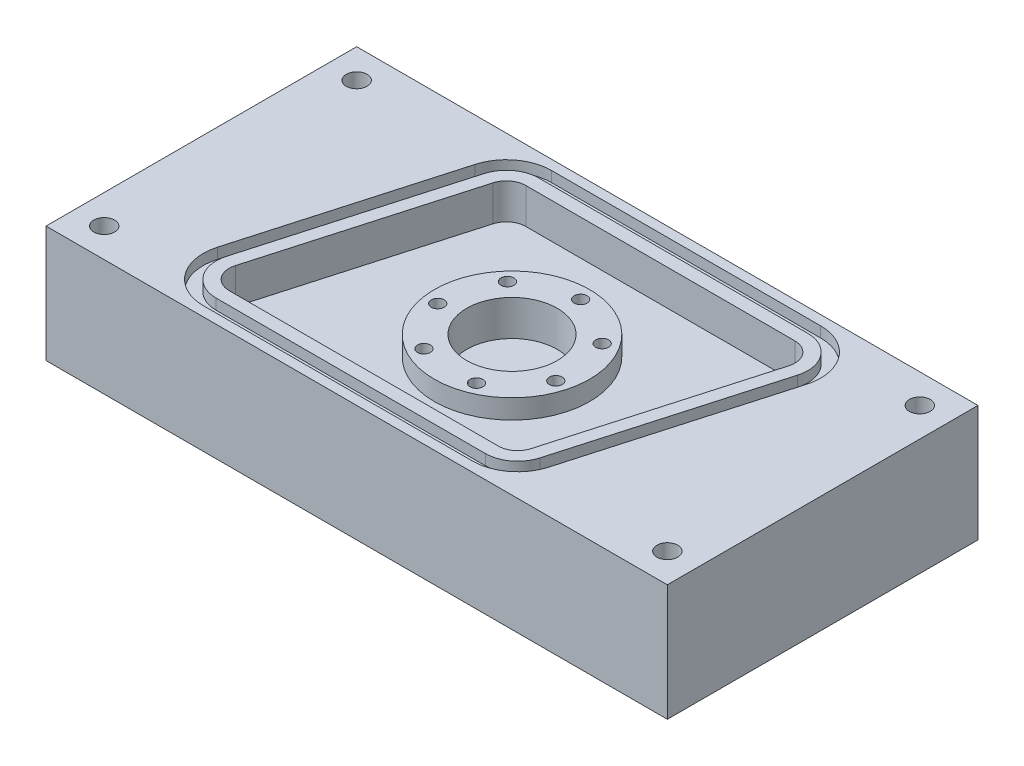
SolidWorks part; units mm, degrees
ref_plane "Front Plane" through (0, 0, 0) normal (0, 0, 1) x (1, 0, 0)
ref_plane "Top Plane" through (0, 0, 0) normal (0, 1, 0) x (1, 0, 0)
ref_plane "Right Plane" through (0, 0, 0) normal (1, 0, 0) x (0, 0, -1)
sketch "Sketch1" plane through (0, 0, 0) normal (0, 1, 0) x (1, 0, 0)
  line L1 (-76.2, 38.1) -> (76.2, 38.1)
  line L2 (-76.2, 38.1) -> (-76.2, -38.1)
  line L3 (-76.2, -38.1) -> (76.2, -38.1)
  line L4 (76.2, 38.1) -> (76.2, -38.1)
  line L5 (-76.2, 38.1) -> (76.2, -38.1) construction
  line L6 (-76.2, -38.1) -> (76.2, 38.1) construction
  point P0 (0, 0)
  dimension "D1" = 152.4
  dimension "D2" = 76.2
extrude "Boss-Extrude1" add sketch "Sketch1" along normal blind 28.575
hole_wizard "#7 (0.201) Diameter Hole1" positions "Sketch3" profile "Sketch2" hole size "#7" standard "ANSI Inch"
sketch "Sketch3" plane through (0, 28.575, 0) normal (0, 1, 0) x (-1, 0, 0)
  line L0 (76.2, -38.1) -> (76.2, 38.1) construction
  line L1 (-76.2, 38.1) -> (-76.2, -38.1) construction
  line L2 (-76.2, -38.1) -> (76.2, -38.1) construction
  line L3 (76.2, 38.1) -> (-76.2, 38.1) construction
  point P0 (69.0626, -30.9626)
  point P1 (69.0626, 30.9626)
  point P3 (-69.0626, 30.9626)
  point P5 (-69.0626, -30.9626)
  dimension "D1" = 7.1374
  dimension "D2" = 7.1374
  dimension "D3" = 7.1374
  dimension "D4" = 7.1374
  dimension "D5" = 7.1374
  dimension "D6" = 7.1374
  dimension "D7" = 7.1374
  dimension "D8" = 7.1374
sketch "Sketch2" plane through (-69.0626, 28.575, -30.9626) normal (1, 0, 0) x (0, 0, 1)
  line L0 (0, 0) -> (0, 14.2338)
  line L1 (0, 14.2338) -> (2.5527, 12.7)
  line L2 (2.5527, 12.7) -> (2.5527, 0)
  line L5 (2.5527, 0) -> (0, 0)
  line L10 (0, 14.2338) -> (-2.5527, 12.7) construction
  line L11 (0, -6.35) -> (0, 107.95) construction
  dimension "Hole Dia." = 5.1054
  dimension "Hole Depth" = 12.7
  dimension "Drill Angle" = 118
sketch "Sketch4" plane through (0, 28.575, 0) normal (0, 1, 0) x (1, 0, 0)
  line L0 (-76.2, 38.1) -> (-76.2, -38.1) construction
  line L1 (76.2, 38.1) -> (-76.2, 38.1) construction
  circle A0 centre (0, 0) radius 11.1125
  dimension "D1" = 76.2
  dimension "D2" = 38.1
extrude "Cut-Extrude1" cut sketch "Sketch4" against normal blind 12.7
hole_wizard "1/8 (0.125) Diameter Hole2" positions "Sketch15" profile "Sketch14" hole size "1/8" standard "ANSI Inch"
sketch "Sketch15" plane through (0, 28.575, 0) normal (0, 1, 0) x (-1, 0, 0)
  line L0 (0, 0) -> (0, -47.9287) construction
  line L2 (0, 0) -> (-61.0436, 0) construction
  line L4 (0, 0) -> (-43.473, -30.4401) construction
  circle A0 centre (0, 0) radius 15.875
  point P0 (-13.004, -9.1055)
  dimension "D1" = 35
sketch "Sketch14" plane through (13.004, 28.575, -9.1055) normal (1, 0, 0) x (0, 0, 1)
  line L0 (0, 0) -> (0, 13.6539)
  line L1 (0, 13.6539) -> (1.5875, 12.7)
  line L2 (1.5875, 12.7) -> (1.5875, 0)
  line L5 (1.5875, 0) -> (0, 0)
  line L10 (0, 13.6539) -> (-1.5875, 12.7) construction
  line L11 (0, -6.35) -> (0, 107.95) construction
  dimension "Hole Dia." = 3.175
  dimension "Hole Depth" = 12.7
  dimension "Drill Angle" = 118
pattern_circular "CirPattern2" count 7 over 360 about axis through (0, 0, 0) along (0, 1, 0) of "1/8 (0.125) Diameter Hole2"
sketch "Sketch9" plane through (0, 28.575, 0) normal (0, 1, 0) x (1, 0, 0)
  circle A0 centre (0, 0) radius 19.05
extrude "Cut-Extrude5" cut sketch "Sketch9" against normal blind 3.9624
sketch "Sketch10" plane through (0, 28.575, 0) normal (0, 1, 0) x (1, 0, 0)
  line L0 (-25.9842, 29.3624) -> (40.005, 29.3624)
  line L1 (-40.005, -29.3624) -> (25.9842, -29.3624)
  line L2 (76.2, 38.1) -> (-76.2, 38.1) construction
  line L3 (-76.2, -38.1) -> (76.2, -38.1) construction
  line L4 (-30.5643, 25.9051) -> (-44.5851, -23.2947)
  line L5 (30.5643, -25.9051) -> (44.5851, 23.2947)
  arc A0 (40.005, 29.3624) -> (44.5851, 23.2947) centre (40.005, 24.5999) cw
  arc A1 (30.5643, -25.9051) -> (25.9842, -29.3624) centre (25.9842, -24.5999) cw
  arc A2 (-40.005, -29.3624) -> (-44.5851, -23.2947) centre (-40.005, -24.5999) cw
  arc A3 (-25.9842, 29.3624) -> (-30.5643, 25.9051) centre (-25.9842, 24.5999) ccw
  circle A4 centre (0, 0) radius 19.05
  circle A5 centre (0, 0) radius 11.1125 construction
  dimension "D5" = 4.7625
  dimension "D3" = 25.9842
  dimension "D4" = 25.9842
  dimension "D6" = 40.005
  dimension "D7" = 40.005
  dimension "D1" = 8.7376
  dimension "D2" = 8.7376
extrude "Cut-Extrude6" cut sketch "Sketch10" against normal blind 8.7122
sketch "Sketch11" plane through (0, 28.575, 0) normal (0, 1, 0) x (1, 0, 0)
  line L2 (-33.6178, 26.7753) -> (-47.6386, -22.4245)
  line L3 (-33.6178, 26.7753) -> (-47.6386, -22.4245)
  line L5 (40.005, 32.5374) -> (-25.9842, 32.5374)
  line L6 (40.005, 32.5374) -> (-25.9842, 32.5374)
  line L8 (33.6178, -26.7753) -> (47.6386, 22.4245)
  line L9 (33.6178, -26.7753) -> (47.6386, 22.4245)
  line L10 (-36.6712, 27.6455) -> (-50.692, -21.5543)
  line L11 (-40.005, -32.5374) -> (25.9842, -32.5374)
  line L12 (-40.005, -32.5374) -> (25.9842, -32.5374)
  line L13 (-40.005, -35.7124) -> (25.9842, -35.7124)
  line L14 (36.6712, -27.6455) -> (50.692, 21.5543)
  line L15 (40.005, 35.7124) -> (-25.9842, 35.7124)
  arc A2 (-47.6386, -22.4245) -> (-40.005, -32.5374) centre (-40.005, -24.5999) ccw
  arc A3 (-47.6386, -22.4245) -> (-40.005, -32.5374) centre (-40.005, -24.5999) ccw
  arc A12 (-25.9842, 32.5374) -> (-33.6178, 26.7753) centre (-25.9842, 24.5999) ccw
  arc A13 (-25.9842, 32.5374) -> (-33.6178, 26.7753) centre (-25.9842, 24.5999) ccw
  arc A15 (47.6386, 22.4245) -> (40.005, 32.5374) centre (40.005, 24.5999) ccw
  arc A16 (47.6386, 22.4245) -> (40.005, 32.5374) centre (40.005, 24.5999) ccw
  arc A17 (-50.692, -21.5543) -> (-40.005, -35.7124) centre (-40.005, -24.5999) ccw
  arc A18 (25.9842, -32.5374) -> (33.6178, -26.7753) centre (25.9842, -24.5999) ccw
  arc A19 (25.9842, -32.5374) -> (33.6178, -26.7753) centre (25.9842, -24.5999) ccw
  arc A20 (25.9842, -35.7124) -> (36.6712, -27.6455) centre (25.9842, -24.5999) ccw
  arc A21 (50.692, 21.5543) -> (40.005, 35.7124) centre (40.005, 24.5999) ccw
  arc A22 (-25.9842, 35.7124) -> (-36.6712, 27.6455) centre (-25.9842, 24.5999) ccw
  dimension "D1" = 3.175
  dimension "D2" = 3.175
  dimension "D3" = 3.175
  dimension "D4" = 3.175
  dimension "D5" = 3.175
  dimension "D6" = 3.175
  dimension "D7" = 3.175
  dimension "D8" = 3.175
  dimension "D9" = 3.175
extrude "Cut-Extrude7" cut sketch "Sketch11" against normal blind 2.5908
